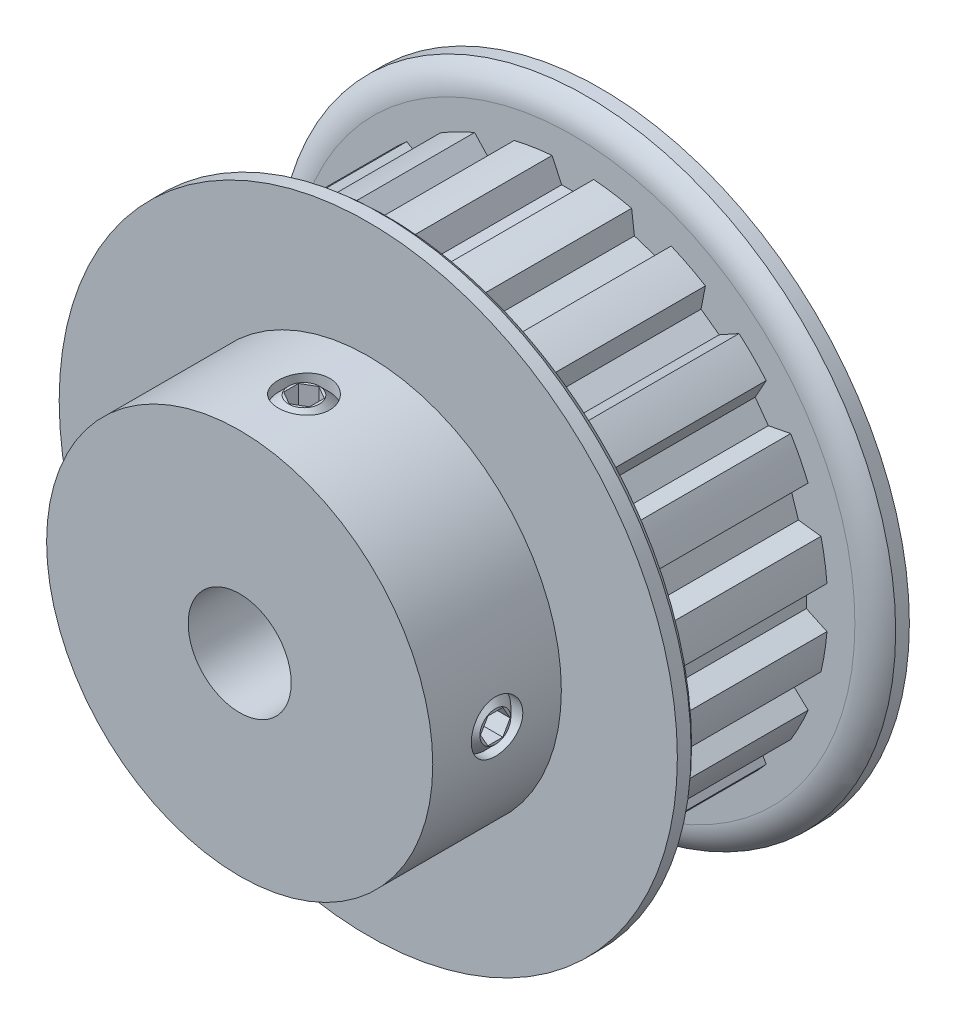
SolidWorks part; units mm, degrees
ref_plane "Front Plane" through (0, 0, 0) normal (0, 0, 1) x (1, 0, 0)
ref_plane "Top Plane" through (0, 0, 0) normal (0, 1, 0) x (1, 0, 0)
ref_plane "Right Plane" through (0, 0, 0) normal (1, 0, 0) x (0, 0, -1)
sketch "Sketch1" plane through (0, 0, 0) normal (0, 0, 1) x (1, 0, 0)
  line L0 (-1.2827, 15.6591) -> (-0.6905, 14.3891)
  line L1 (-0.6905, 14.3891) -> (0.6905, 14.3891)
  line L2 (0.6905, 14.3891) -> (1.2827, 15.6591)
  line L3 (-1.2827, 15.6591) -> (1.2827, 15.6591)
  line L4 (0, 0) -> (0, 14.3891) construction
  line L5 (0, 14.3891) -> (0, 16.6751) construction
  circle A0 centre (0, 0) radius 16.1671 construction
  circle A1 centre (0, 0) radius 19.05 construction
  circle A2 centre (0, 0) radius 15.7115 construction
  point P6 (0, 15.6591)
  point P11 (0, 16.1671)
  point P13 (0, 19.05)
  point P14 (0, 15.7115)
  dimension "D1" = 1.016
  dimension "D2" = 0.508
sketch "Sketch2" plane through (0, 0, 0) normal (1, 0, 0) x (0, 0, -1)
  line L0 (-11.1125, 3.175) -> (11.1125, 3.175)
  line L1 (-11.1125, 3.175) -> (-11.1125, 11.8999)
  line L2 (-11.1125, 11.8999) -> (-3.1877, 11.8999)
  line L3 (-3.1877, 11.8999) -> (-3.1877, 19.05)
  line L4 (-3.1877, 19.05) -> (-1.4986, 19.05) construction
  line L5 (-1.4986, 19.05) -> (-1.4986, 15.7115) construction
  line L6 (-1.4986, 15.7115) -> (9.4234, 15.7115)
  line L7 (9.4234, 15.7115) -> (9.4234, 19.05) construction
  line L8 (9.4234, 19.05) -> (11.1125, 19.05) construction
  line L9 (11.1125, 19.05) -> (11.1125, 3.175)
  line L10 (-11.1125, 0) -> (11.1125, 0) construction
  line L13 (-3.1877, 19.05) -> (-2.3431, 19.05)
  line L14 (-1.4986, 17.3808) -> (-1.4986, 15.7115)
  line L15 (9.4234, 15.7115) -> (9.4234, 17.3808)
  line L16 (10.268, 19.05) -> (11.1125, 19.05)
  arc A0 (-1.4986, 17.3808) -> (-2.3431, 19.05) centre (-3.5705, 17.3808) ccw
  arc A1 (9.4234, 17.3808) -> (10.268, 19.05) centre (11.4953, 17.3808) cw
  point P12 (-1.4986, 17.3808)
  point P14 (-2.3431, 19.05)
  point P20 (9.4234, 17.3808)
  point P21 (10.268, 19.05)
  point P25 (9.4234, 0)
  point P26 (-1.4986, 0)
  dimension "Bore" = 6.35
  dimension "Hub Dia" = 23.7998
  dimension "Outside Width" = 14.3002
  dimension "Inside Width" = 10.922
revolve "Revolve1" add sketch "Sketch2" angle 360 mid plane about L10
sketch "Sketch3" plane through (0, 0, 0) normal (0, 0, 1) x (1, 0, 0)
  line L0 (-0.6905, 14.3891) -> (0.6905, 14.3891) construction
  line L1 (0.6905, 14.3891) -> (1.2827, 15.6591) construction
  line L2 (-1.2827, 15.6591) -> (-0.6905, 14.3891) construction
  line L3 (-0.6905, 14.3891) -> (0.6905, 14.3891)
  line L4 (0.6905, 14.3891) -> (1.2827, 15.6591)
  line L5 (-1.2827, 15.6591) -> (-0.6905, 14.3891)
  circle A0 centre (0, 0) radius 15.7115 construction
  arc A1 (1.2827, 15.6591) -> (-1.2827, 15.6591) centre (0, 0) ccw
extrude "Cut-Extrude1" cut sketch "Sketch3" against normal up to vertex (9.4234 mm away) from vertex at 1.4986 starting at point (0, 15.7115, 1.4986)
pattern_circular "CirPattern1" count 20 over 360 about axis through (0, 0, 0) along (0, 0, 1) of "Cut-Extrude1"
sketch "Sketch4" plane through (0, 0, 0) normal (0, 1, 0) x (1, 0, 0)
  line L0 (0, -3.1877) -> (0, -11.1125) construction
  line L1 (-11.8999, -3.1877) -> (11.8999, -3.1877) construction
  line L2 (-11.8999, -11.1125) -> (11.8999, -11.1125) construction
  circle A0 centre (0, -7.1501) radius 1.5875
  dimension "D1" = 3.175
extrude "Cut-Extrude2" cut sketch "Sketch4" along normal through all
ref_plane "Plane1" through (0, 0, 7.1501) normal (0, 0, 1) x (1, 0, 0)
sketch "Sketch5" plane through (0, 0, 7.1501) normal (0, 0, 1) x (1, 0, 0)
  line L0 (0, 0) -> (0, 11.8999) construction
  line L1 (-1.5875, 11.7935) -> (-1.5875, 2.7496) construction
  line L2 (-1.5875, 11.7935) -> (-1.5875, 2.7496) construction
  line L3 (0, 11.7935) -> (0, 3.175)
  line L4 (0, 3.175) -> (-0.9525, 3.175)
  line L5 (-1.5875, 11.1585) -> (-1.5875, 3.81)
  line L6 (-0.9525, 11.7935) -> (0, 11.7935)
  line L7 (-1.5875, 11.1585) -> (-0.9525, 11.7935)
  line L8 (-1.5875, 3.81) -> (-0.9525, 3.175)
  circle A0 centre (0, 0) radius 11.8999 construction
  circle A3 centre (0, 0) radius 3.175 construction
  point P13 (-1.5875, 3.175)
  point P15 (-1.5875, 11.7935)
revolve "Revolve2" add sketch "Sketch5" angle 360 mid plane about L0
sketch "Sketch6" plane through (0, 11.7935, 0) normal (0, -1, 0) x (-1, 0, 0)
  line L1 (0, -6.2336) -> (-0.7938, -6.6918)
  line L2 (-0.7938, -6.6918) -> (-0.7937, -7.6084)
  line L3 (-0.7937, -7.6084) -> (0, -8.0666)
  line L4 (0, -8.0666) -> (0.7938, -7.6084)
  line L5 (0.7938, -7.6084) -> (0.7938, -6.6918)
  line L6 (0.7938, -6.6918) -> (0, -6.2336)
  circle A0 centre (0, -7.1501) radius 0.7938 construction
  dimension "D1" = 1.5875
extrude "Cut-Extrude3" cut sketch "Sketch6" along normal blind 1.1906
pattern_circular "CirPattern2" count 2 every 90 about axis through (0, 0, 0) along (0, 0, 1) of "Cut-Extrude2", "Revolve2", "Cut-Extrude3"
equation "\"D2@Sketch1\" = \"D1@Sketch1\"/2"
equation "\"D1@Sketch4\" = \"Bore@Sketch2\"/2"
equation "\"D1@Sketch6\" = \"D1@Sketch4\"/2"
equation "\"D1@Cut-Extrude3\" = \"D1@Sketch6\"*.75"
